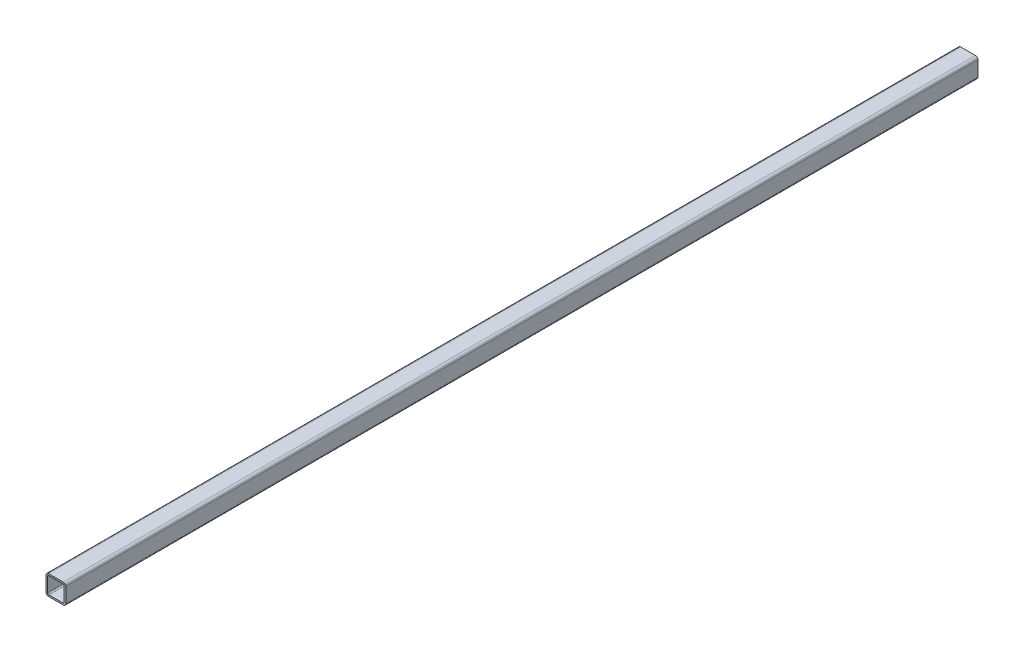
SolidWorks part; units mm, degrees
ref_plane "Front Plane" through (0, 0, 0) normal (0, 0, 1) x (1, 0, 0)
ref_plane "Top Plane" through (0, 0, 0) normal (0, 1, 0) x (1, 0, 0)
ref_plane "Right Plane" through (0, 0, 0) normal (1, 0, 0) x (0, 0, -1)
sketch "Sketch1" plane through (0, 0, 0) normal (0, 0, 1) x (1, 0, 0)
  line L0 (-10.668, -10.668) -> (-10.668, 10.668)
  line L1 (12.7, -12.7) -> (-12.7, -12.7)
  line L2 (12.7, -12.7) -> (12.7, 12.7)
  line L3 (12.7, 12.7) -> (-12.7, 12.7)
  line L4 (-12.7, -12.7) -> (-12.7, 12.7)
  line L5 (12.7, -12.7) -> (-12.7, 12.7) construction
  line L6 (12.7, 12.7) -> (-12.7, -12.7) construction
  line L7 (10.668, 10.668) -> (-10.668, 10.668)
  line L8 (10.668, -10.668) -> (10.668, 10.668)
  line L9 (10.668, -10.668) -> (-10.668, -10.668)
  point P0 (0, 0)
  dimension "Rail Width" = 25.4
  dimension "Rail Height" = 25.4
  dimension "Wall Thickness" = 2.032
sketch "Sketch2" plane through (0, 0, 0) normal (1, 0, 0) x (0, 0, -1)
  line L0 (-609.6, 0) -> (609.6, 0) construction
  line L1 (-609.6, -12.7) -> (-609.6, 12.7) construction
  line L2 (609.6, -12.7) -> (609.6, 12.7) construction
  point P0 (-577.85, 0)
  point P3 (577.85, 0)
  point P4 (0, 0)
  point P9 (-609.6, 0)
  point P12 (609.6, 0)
  dimension "D1" = 31.75
  dimension "D2" = 31.75
  dimension "D3" = 25.4
  dimension "Length" = 1219.2
sketch "Sketch3" plane through (0, 0, 0) normal (0, 0, 1) x (1, 0, 0)
  line L0 (10.668, -10.668) -> (-10.668, -10.668) construction
  line L1 (10.668, -10.668) -> (10.668, 10.668) construction
  line L2 (10.668, 10.668) -> (-10.668, 10.668) construction
  line L3 (-10.668, -10.668) -> (-10.668, 10.668) construction
  line L4 (12.7, -12.7) -> (-12.7, -12.7) construction
  line L5 (12.7, -12.7) -> (12.7, 12.7) construction
  line L6 (12.7, 12.7) -> (-12.7, 12.7) construction
  line L7 (-12.7, -12.7) -> (-12.7, 12.7) construction
  line L8 (10.668, -10.668) -> (-10.668, -10.668)
  line L9 (10.668, -10.668) -> (10.668, 10.668)
  line L10 (10.668, 10.668) -> (-10.668, 10.668)
  line L11 (-10.668, -10.668) -> (-10.668, 10.668)
  line L12 (12.7, -12.7) -> (-12.7, -12.7)
  line L13 (12.7, -12.7) -> (12.7, 12.7)
  line L14 (12.7, 12.7) -> (-12.7, 12.7)
  line L15 (-12.7, -12.7) -> (-12.7, 12.7)
extrude "Boss-Extrude1" add sketch "Sketch3" along normal up to vertex (609.6 mm away) and the other way up to vertex (609.6 mm away) up to point (0, 0, 609.6) other way up to point (0, 0, -609.6)
fillet "Fillet1" radius 3.175 4 edges at (-12.7, -12.7, 0) (12.7, -12.7, 0) (-12.7, 12.7, 0) (12.7, 12.7, 0)
fillet "Fillet2" radius 1.5875 4 edges at (10.668, -10.668, 0) (10.668, 10.668, 0) (-10.668, -10.668, 0) (-10.668, 10.668, 0)
sketch "Sketch4" plane through (0, 12.7, 0) normal (0, 1, 0) x (1, 0, 0)
  line L0 (12.7, 609.6) -> (12.7, -609.6) construction
  line L1 (-12.7, 609.6) -> (12.7, 609.6)
  line L2 (-12.7, 609.6) -> (-12.7, 558.8)
  line L3 (-12.7, 558.8) -> (12.7, 558.8)
  line L4 (12.7, 609.6) -> (12.7, 558.8)
  dimension "D1" = 50.8
extrude "Cut-Extrude1" cut sketch "Sketch4" against normal through all
equation "\"D1@Sketch2\"=\"Rail Width@Sketch1\"*1.25"
equation "\"D2@Sketch2\"=\"D1@Sketch2\""
equation "\"D3@Sketch2\"=\"Rail Height@Sketch1\""
equation "\"D1@Fillet1\"=\"Rail Width@Sketch1\"*.125"
equation "\"D1@Fillet2\"=\"Rail Width@Sketch1\"*.0625"
